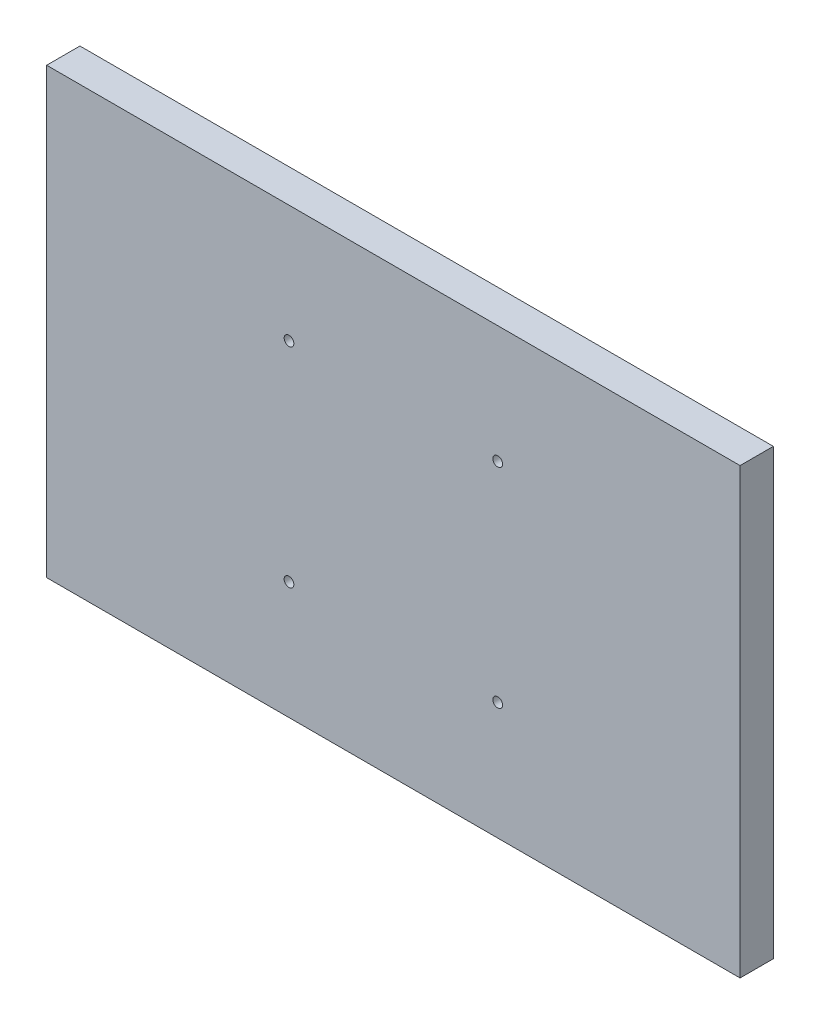
SolidWorks part; units mm, degrees
ref_plane "前视基准面" through (0, 0, 0) normal (0, 0, 1) x (1, 0, 0)
ref_plane "上视基准面" through (0, 0, 0) normal (0, 1, 0) x (1, 0, 0)
ref_plane "右视基准面" through (0, 0, 0) normal (1, 0, 0) x (0, 0, -1)
sketch "草图1" plane through (0, 0, 0) normal (0, 0, 1) x (1, 0, 0)
  line L1 (-125, 80) -> (125, 80)
  line L2 (-125, 80) -> (-125, -80)
  line L3 (-125, -80) -> (125, -80)
  line L4 (125, 80) -> (125, -80)
  line L5 (-125, 80) -> (125, -80) construction
  line L6 (-125, -80) -> (125, 80) construction
  line L7 (-37.625, 37.625) -> (37.625, 37.625) construction
  line L8 (-37.625, 37.625) -> (-37.625, -37.625) construction
  line L9 (-37.625, -37.625) -> (37.625, -37.625) construction
  line L10 (37.625, 37.625) -> (37.625, -37.625) construction
  line L11 (-37.625, 37.625) -> (37.625, -37.625) construction
  line L12 (-37.625, -37.625) -> (37.625, 37.625) construction
  circle A0 centre (37.625, 37.625) radius 1.75
  circle A1 centre (37.625, -37.625) radius 1.75
  circle A2 centre (-37.625, -37.625) radius 1.75
  circle A3 centre (-37.625, 37.625) radius 1.75
  point P0 (0, 0)
  point P6 (0, 0)
  dimension "D3" = 3.5
  dimension "D4" = 3.5
  dimension "D5" = 3.5
  dimension "D6" = 3.5
  dimension "D1" = 250
  dimension "D2" = 160
  dimension "D7" = 75.25
  dimension "D8" = 75.25
extrude "凸台-拉伸1" add sketch "草图1" along normal blind 12
